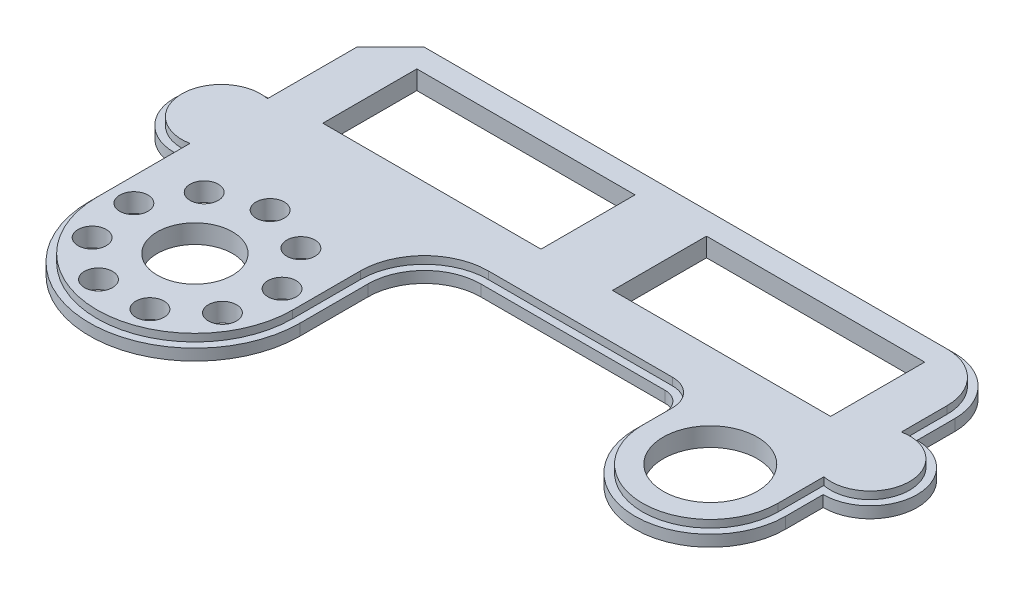
SolidWorks part; units mm, degrees
material "NEOPRENE"
ref_plane "Front" through (0, 0, 0) normal (0, 0, 1) x (1, 0, 0)
ref_plane "Top" through (0, 0, 0) normal (0, 1, 0) x (1, 0, 0)
ref_plane "Right" through (0, 0, 0) normal (1, 0, 0) x (0, 0, -1)
sketch "Sketch1" plane through (0, 0, 0) normal (0, 1, 0) x (1, 0, 0)
  line L0 (0, -12.7) -> (0, -101.6)
  line L1 (71.12, -101.6) -> (71.12, -78.74)
  line L2 (90.17, -59.69) -> (152.4, -59.69)
  line L3 (158.75, -66.04) -> (158.75, -76.2)
  line L4 (209.55, -76.2) -> (209.55, -19.05)
  line L5 (190.5, 0) -> (12.7, 0)
  line L6 (12.7, 0) -> (0, -12.7)
  line L7 (19.05, -10.16) -> (92.71, -10.16)
  line L8 (19.05, -10.16) -> (19.05, -41.91)
  line L9 (19.05, -41.91) -> (92.71, -41.91)
  line L10 (92.71, -10.16) -> (92.71, -41.91)
  line L11 (19.05, -10.16) -> (92.71, -41.91) construction
  line L12 (19.05, -41.91) -> (92.71, -10.16) construction
  line L13 (116.84, -10.16) -> (190.5, -10.16)
  line L14 (116.84, -10.16) -> (116.84, -41.91)
  line L15 (116.84, -41.91) -> (190.5, -41.91)
  line L16 (190.5, -10.16) -> (190.5, -41.91)
  line L17 (116.84, -10.16) -> (190.5, -41.91) construction
  line L18 (116.84, -41.91) -> (190.5, -10.16) construction
  arc A0 (0, -101.6) -> (71.12, -101.6) centre (35.56, -101.6) ccw
  arc A1 (71.12, -78.74) -> (90.17, -59.69) centre (90.17, -78.74) cw
  arc A2 (152.4, -59.69) -> (158.75, -66.04) centre (152.4, -66.04) cw
  arc A3 (158.75, -76.2) -> (209.55, -76.2) centre (184.15, -76.2) ccw
  circle A4 centre (35.56, -101.6) radius 12.7
  circle A5 centre (184.15, -76.2) radius 15.875
  arc A6 (209.55, -19.05) -> (190.5, 0) centre (190.5, -19.05) ccw
  circle A7 centre (0, -57.15) radius 15.875
  circle A8 centre (209.55, -47.625) radius 15.875
  point P0 (0, 0)
  point P14 (55.88, -26.035)
  point P20 (153.67, -26.035)
  point P35 (0, 0)
  dimension "D1" = 19.05
  dimension "D5" = 76.2
  dimension "D6" = 31.75
  dimension "D7" = 31.75
  dimension "D8" = 25.4
  dimension "D9" = 35.56
  dimension "D10" = 25.4
  dimension "D17" = 6.35
  dimension "D18" = 19.05
  dimension "D2" = 73.66
  dimension "D3" = 31.75
  dimension "D11" = 101.6
  dimension "D12" = 19.05
  dimension "D13" = 209.55
  dimension "D14" = 10.16
  dimension "D15" = 17.78
  dimension "D16" = 19.05
extrude "Boss-Extrude2" add sketch "Sketch1" along normal blind 6.35 contours A8 L4 A6 L5 L6 L0 A7 A0 L1 A1 L2 A2 L3 A3 L13 L16 L15 L14 L7 L10 L9 L8 A4 A5 | L0 A7 | L0 A7 | L4 A8 | L4 A8
sketch "Sketch2" plane through (0, 6.35, 0) normal (0, 1, 0) x (1, 0, 0)
  line L0 (2.54, -13.7521) -> (2.54, -44.0591)
  line L1 (2.54, -70.2409) -> (2.54, -101.6)
  line L2 (68.58, -101.6) -> (68.58, -78.74)
  line L3 (90.17, -57.15) -> (152.4, -57.15)
  line L4 (161.29, -66.04) -> (161.29, -76.2)
  line L5 (207.01, -76.2) -> (207.01, -60.7159)
  line L6 (207.01, -34.5341) -> (207.01, -19.05)
  line L7 (190.5, -2.54) -> (13.7521, -2.54)
  line L8 (13.7521, -2.54) -> (2.54, -13.7521)
  line L9 (209.55, -76.2) -> (209.55, -63.5)
  line L10 (209.55, -31.75) -> (209.55, -19.05)
  line L11 (190.5, 0) -> (12.7, 0)
  line L12 (12.7, 0) -> (0, -12.7)
  line L13 (0, -12.7) -> (0, -41.275)
  line L14 (0, -73.025) -> (0, -101.6)
  line L15 (71.12, -101.6) -> (71.12, -78.74)
  line L16 (90.17, -59.69) -> (152.4, -59.69)
  line L17 (158.75, -66.04) -> (158.75, -76.2)
  line L18 (209.55, -76.2) -> (209.55, -63.5)
  line L19 (209.55, -31.75) -> (209.55, -19.05)
  line L20 (190.5, 0) -> (12.7, 0)
  line L21 (12.7, 0) -> (0, -12.7)
  line L22 (0, -12.7) -> (0, -41.275)
  line L23 (0, -73.025) -> (0, -101.6)
  line L24 (71.12, -101.6) -> (71.12, -78.74)
  line L25 (90.17, -59.69) -> (152.4, -59.69)
  line L26 (158.75, -66.04) -> (158.75, -76.2)
  arc A0 (2.54, -44.0591) -> (2.54, -70.2409) centre (0, -57.15) ccw
  arc A1 (2.54, -101.6) -> (68.58, -101.6) centre (35.56, -101.6) ccw
  arc A2 (90.17, -57.15) -> (68.58, -78.74) centre (90.17, -78.74) ccw
  arc A3 (161.29, -66.04) -> (152.4, -57.15) centre (152.4, -66.04) ccw
  arc A4 (161.29, -76.2) -> (207.01, -76.2) centre (184.15, -76.2) ccw
  arc A5 (207.01, -60.7159) -> (207.01, -34.5341) centre (209.55, -47.625) ccw
  arc A6 (207.01, -19.05) -> (190.5, -2.54) centre (190.5, -19.05) ccw
  arc A7 (209.55, -63.5) -> (209.55, -31.75) centre (209.55, -47.625) ccw
  arc A8 (209.55, -19.05) -> (190.5, 0) centre (190.5, -19.05) ccw
  arc A9 (0, -41.275) -> (0, -73.025) centre (0, -57.15) ccw
  arc A10 (0, -101.6) -> (71.12, -101.6) centre (35.56, -101.6) ccw
  arc A11 (90.17, -59.69) -> (71.12, -78.74) centre (90.17, -78.74) ccw
  arc A12 (158.75, -66.04) -> (152.4, -59.69) centre (152.4, -66.04) ccw
  arc A13 (158.75, -76.2) -> (209.55, -76.2) centre (184.15, -76.2) ccw
  arc A14 (209.55, -63.5) -> (209.55, -31.75) centre (209.55, -47.625) ccw
  arc A15 (209.55, -19.05) -> (190.5, 0) centre (190.5, -19.05) ccw
  arc A16 (0, -41.275) -> (0, -73.025) centre (0, -57.15) ccw
  arc A17 (0, -101.6) -> (71.12, -101.6) centre (35.56, -101.6) ccw
  arc A18 (90.17, -59.69) -> (71.12, -78.74) centre (90.17, -78.74) ccw
  arc A19 (158.75, -66.04) -> (152.4, -59.69) centre (152.4, -66.04) ccw
  arc A20 (158.75, -76.2) -> (209.55, -76.2) centre (184.15, -76.2) ccw
  dimension "D1" = 0
  dimension "D2" = 2.54
extrude "Cut-Extrude1" cut sketch "Sketch2" against normal blind 2.54
sketch "Sketch3" plane through (0, 6.35, 0) normal (0, 1, 0) x (1, 0, 0)
  circle A0 centre (35.56, -101.6) radius 25.4 construction
  circle A1 centre (35.56, -76.2) radius 4.7625
  dimension "D1" = 50.8
  dimension "D2" = 9.525
extrude "Cut-Extrude2" cut sketch "Sketch3" against normal through all
pattern_circular "CirPattern1" count 9 over 360 about axis through (35.56, 0, 101.6) along (0, 1, 0) of "Cut-Extrude2"
